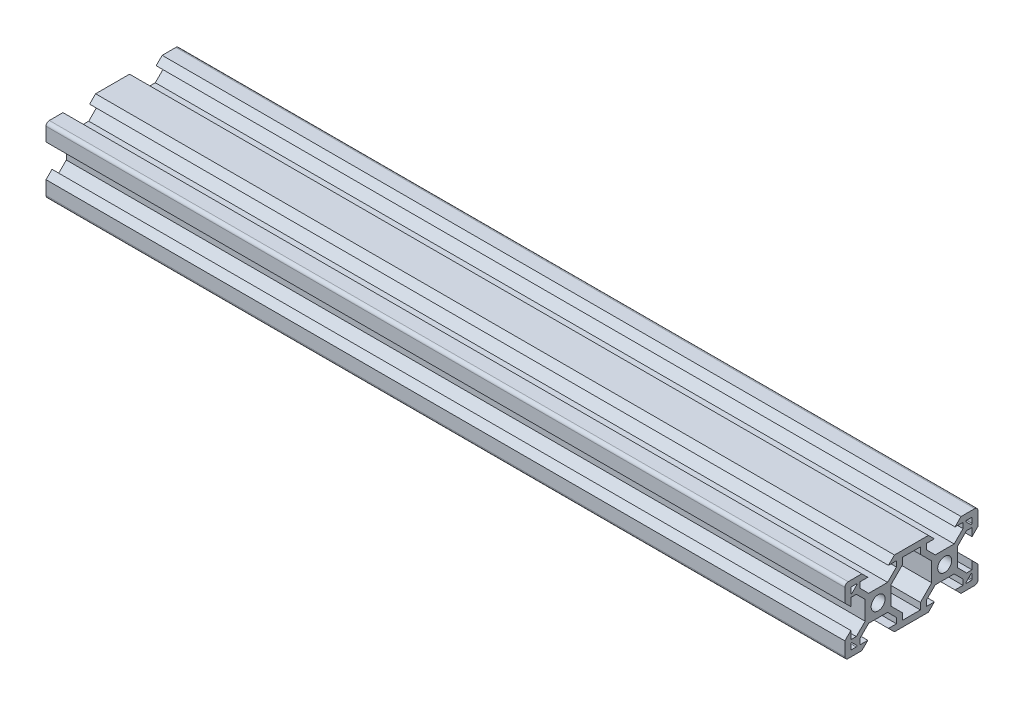
SolidWorks part; units mm, degrees
material "1060 Alloy"
ref_plane "Front Plane" through (0, 0, 0) normal (0, 0, 1) x (1, 0, 0)
ref_plane "Top Plane" through (0, 0, 0) normal (0, 1, 0) x (1, 0, 0)
ref_plane "Right Plane" through (0, 0, 0) normal (1, 0, 0) x (0, 0, -1)
sketch "Sketch4" plane through (0, 0, 0) normal (1, 0, 0) x (0, 0, -1)
  line L0 (-19.2399, 7.0114) -> (20.7601, 7.0114) construction
  dimension "D1" = 40
sketch "Sketch5" plane through (0, 0, 0) normal (1, 0, 0) x (0, 0, -1)
  line L0 (-19.998, 4.9) -> (-18.198, 3.1)
  line L1 (-18.198, 3.1) -> (-18.198, 5.4993)
  line L2 (-18.198, 5.4993) -> (-16.558, 5.4993)
  line L3 (-16.558, 5.4993) -> (-13.9, 2.8413)
  line L4 (-13.9, 2.8413) -> (-13.9, -2.8387)
  line L5 (-13.9, -2.8387) -> (-16.558, -5.4967)
  line L6 (-16.558, -5.4967) -> (-18.198, -5.4967)
  line L7 (-18.198, -5.4967) -> (-18.198, -3.1)
  line L8 (-18.198, -3.1) -> (-19.998, -4.9)
  line L9 (-19.998, -4.9) -> (-19.998, -9)
  line L10 (-18.998, -10) -> (-14.9, -10)
  line L11 (-14.9, -10) -> (-13.1, -8.2)
  line L12 (-13.1, -8.2) -> (-15.5, -8.2)
  line L13 (-15.5, -8.2) -> (-15.5, -6.56)
  line L14 (-15.5, -6.56) -> (-12.84, -3.9)
  line L15 (-12.84, -3.9) -> (-7.16, -3.9)
  line L16 (-7.16, -3.9) -> (-4.5, -6.56)
  line L17 (-4.5, -6.56) -> (-4.5, -8.2)
  line L18 (-4.5, -8.2) -> (-6.9, -8.2)
  line L19 (-6.9, -8.2) -> (-5.1, -10)
  line L20 (-5.1, -10) -> (5.1, -10)
  line L21 (5.1, -10) -> (6.9, -8.2)
  line L22 (6.9, -8.2) -> (4.496, -8.2)
  line L23 (4.496, -8.2) -> (4.496, -6.56)
  line L24 (4.496, -6.56) -> (7.156, -3.9)
  line L25 (7.156, -3.9) -> (12.836, -3.9)
  line L26 (12.836, -3.9) -> (15.496, -6.56)
  line L27 (15.496, -6.56) -> (15.496, -8.2)
  line L28 (15.496, -8.2) -> (13.1, -8.2)
  line L29 (13.1, -8.2) -> (14.9, -10)
  line L30 (14.9, -10) -> (19.002, -10)
  line L31 (20.002, -9) -> (20.002, -4.9)
  line L32 (20.002, -4.9) -> (18.202, -3.1)
  line L33 (18.202, -3.1) -> (18.202, -5.5046)
  line L34 (18.202, -5.5046) -> (16.562, -5.5046)
  line L35 (16.562, -5.5046) -> (13.9, -2.8426)
  line L36 (13.9, -2.8426) -> (13.9, 2.8374)
  line L37 (13.9, 2.8374) -> (16.562, 5.4993)
  line L38 (16.562, 5.4993) -> (18.202, 5.4993)
  line L39 (18.202, 5.4993) -> (18.202, 3.1)
  line L40 (18.202, 3.1) -> (20.002, 4.9)
  line L41 (20.002, 4.9) -> (20.002, 9)
  line L42 (19.002, 10) -> (14.9, 10)
  line L43 (14.9, 10) -> (13.1, 8.2)
  line L44 (13.1, 8.2) -> (15.5013, 8.2)
  line L45 (15.5013, 8.2) -> (15.5013, 6.56)
  line L46 (15.5013, 6.56) -> (12.8413, 3.9)
  line L47 (12.8413, 3.9) -> (7.1613, 3.9)
  line L48 (7.1613, 3.9) -> (4.5013, 6.56)
  line L49 (4.5013, 6.56) -> (4.5013, 8.2)
  line L50 (4.5013, 8.2) -> (6.9, 8.2)
  line L51 (6.9, 8.2) -> (5.1, 10)
  line L52 (5.1, 10) -> (-5.1, 10)
  line L53 (-5.1, 10) -> (-6.9, 8.2)
  line L54 (-6.9, 8.2) -> (-4.5013, 8.2)
  line L55 (-4.5013, 8.2) -> (-4.5013, 6.56)
  line L56 (-4.5013, 6.56) -> (-7.1613, 3.9)
  line L57 (-7.1613, 3.9) -> (-12.8413, 3.9)
  line L58 (-12.8413, 3.9) -> (-15.5013, 6.56)
  line L59 (-15.5013, 6.56) -> (-15.5013, 8.2)
  line L60 (-15.5013, 8.2) -> (-13.1, 8.2)
  line L61 (-13.1, 8.2) -> (-14.9, 10)
  line L62 (-14.9, 10) -> (-18.998, 10)
  line L63 (-19.998, 9) -> (-19.998, 4.9)
  line L64 (6.1, -2.84) -> (6.1, 2.84)
  line L65 (6.1, 2.84) -> (2.7, 6.24)
  line L66 (2.7, 6.24) -> (2.7, 8.2)
  line L67 (2.7, 8.2) -> (-2.7, 8.2)
  line L68 (-2.7, 8.2) -> (-2.7, 6.24)
  line L69 (-2.7, 6.24) -> (-6.1, 2.84)
  line L70 (-6.1, 2.84) -> (-6.1, -2.84)
  line L71 (-6.1, -2.84) -> (-2.7, -6.24)
  line L72 (-2.7, -6.24) -> (-2.7, -8.2)
  line L73 (-2.7, -8.2) -> (2.7, -8.2)
  line L74 (2.7, -8.2) -> (2.7, -6.24)
  line L75 (2.7, -6.24) -> (6.1, -2.84)
  line L76 (0, -8.2) -> (0, 8.2) construction
  line L77 (6.1, 0) -> (-6.1, 0) construction
  line L78 (16.562, 5.4993) -> (15.5013, 6.56) construction
  line L79 (16.5713, 8.2) -> (18.002, 8.2)
  line L81 (17.8606, 6.4279) -> (16.4299, 7.8586)
  line L82 (18.202, 8) -> (18.202, 6.5693)
  line L83 (18.002, 6.5693) -> (18.002, 8) construction
  line L84 (18.002, 8) -> (16.5713, 8) construction
  line L85 (16.5713, 8) -> (18.002, 6.5693) construction
  line L86 (16.5713, -8.2) -> (18.002, -8.2)
  line L87 (18.202, -8) -> (18.202, -6.5693)
  line L88 (17.8606, -6.4279) -> (16.4299, -7.8586)
  line L89 (-17.8606, 6.4279) -> (-16.4299, 7.8586)
  line L90 (-16.5713, 8.2) -> (-18.002, 8.2)
  line L91 (-18.202, 8) -> (-18.202, 6.5693)
  line L92 (-16.5713, -8.2) -> (-18.002, -8.2)
  line L93 (-17.8606, -6.4279) -> (-16.4299, -7.8586)
  line L94 (-18.202, -8) -> (-18.202, -6.5693)
  circle A0 centre (-10, 0) radius 2.1
  circle A1 centre (10, 0) radius 2.1
  arc A2 (-19.998, -9) -> (-18.998, -10) centre (-18.998, -9) ccw
  arc A5 (-18.998, 10) -> (-19.998, 9) centre (-18.998, 9) ccw
  arc A6 (20.002, -9) -> (19.002, -10) centre (19.002, -9) cw
  arc A7 (20.002, 9) -> (19.002, 10) centre (19.002, 9) ccw
  arc A8 (18.002, 8.2) -> (18.202, 8) centre (18.002, 8) cw
  arc A10 (16.4299, 7.8586) -> (16.5713, 8.2) centre (16.5713, 8) cw
  arc A12 (18.202, 6.5693) -> (17.8606, 6.4279) centre (18.002, 6.5693) cw
  arc A13 (16.4299, -7.8586) -> (16.5713, -8.2) centre (16.5713, -8) ccw
  arc A14 (18.002, -8.2) -> (18.202, -8) centre (18.002, -8) ccw
  arc A15 (18.202, -6.5693) -> (17.8606, -6.4279) centre (18.002, -6.5693) ccw
  arc A16 (-18.202, 6.5693) -> (-17.8606, 6.4279) centre (-18.002, 6.5693) ccw
  arc A17 (-16.4299, 7.8586) -> (-16.5713, 8.2) centre (-16.5713, 8) ccw
  arc A18 (-18.002, 8.2) -> (-18.202, 8) centre (-18.002, 8) ccw
  arc A19 (-18.002, -8.2) -> (-18.202, -8) centre (-18.002, -8) cw
  arc A20 (-16.4299, -7.8586) -> (-16.5713, -8.2) centre (-16.5713, -8) cw
  arc A21 (-18.202, -6.5693) -> (-17.8606, -6.4279) centre (-18.002, -6.5693) cw
  dimension "D1" = 4.2
  dimension "D20" = 3.9
  dimension "D27" = 1
  dimension "D40" = 1
  dimension "D41" = 1
  dimension "D42" = 1
  dimension "D45" = 0.2
  dimension "D47" = 1.07
  dimension "D48" = 1.07
  dimension "D49" = 0.2
  dimension "D2" = 20
  dimension "D3" = 10
  dimension "D4" = 5.68
  dimension "D5" = 5.4
  dimension "D6" = 1.96
  dimension "D7" = 45
  dimension "D8" = 1.8
  dimension "D9" = 1.64
  dimension "D10" = 1.8
  dimension "D11" = 40
  dimension "D12" = 20
  dimension "D13" = 3.9
  dimension "D14" = 1.5
  dimension "D15" = 1.5
  dimension "D16" = 3.9
  dimension "D17" = 3.9
  dimension "D18" = 3.9
  dimension "D19" = 3.9
  dimension "D21" = 1.5
  dimension "D22" = 1.5
  dimension "D23" = 1.64
  dimension "D24" = 45
  dimension "D25" = 1.5
  dimension "D26" = 1.8
  dimension "D28" = 6.2
  dimension "D29" = 6.2
  dimension "D30" = 6.2
  dimension "D31" = 6.2
  dimension "D32" = 6.2
  dimension "D33" = 3.1
  dimension "D34" = 3.1
  dimension "D35" = 3.1
  dimension "D36" = 3.1
  dimension "D37" = 6.2
  dimension "D38" = 3.1
  dimension "D39" = 3.1
  dimension "D43" = 1.64
  dimension "D44" = 135
  dimension "D46" = 45
extrude "Boss-Extrude1" add sketch "Sketch5" along normal mid plane 240
